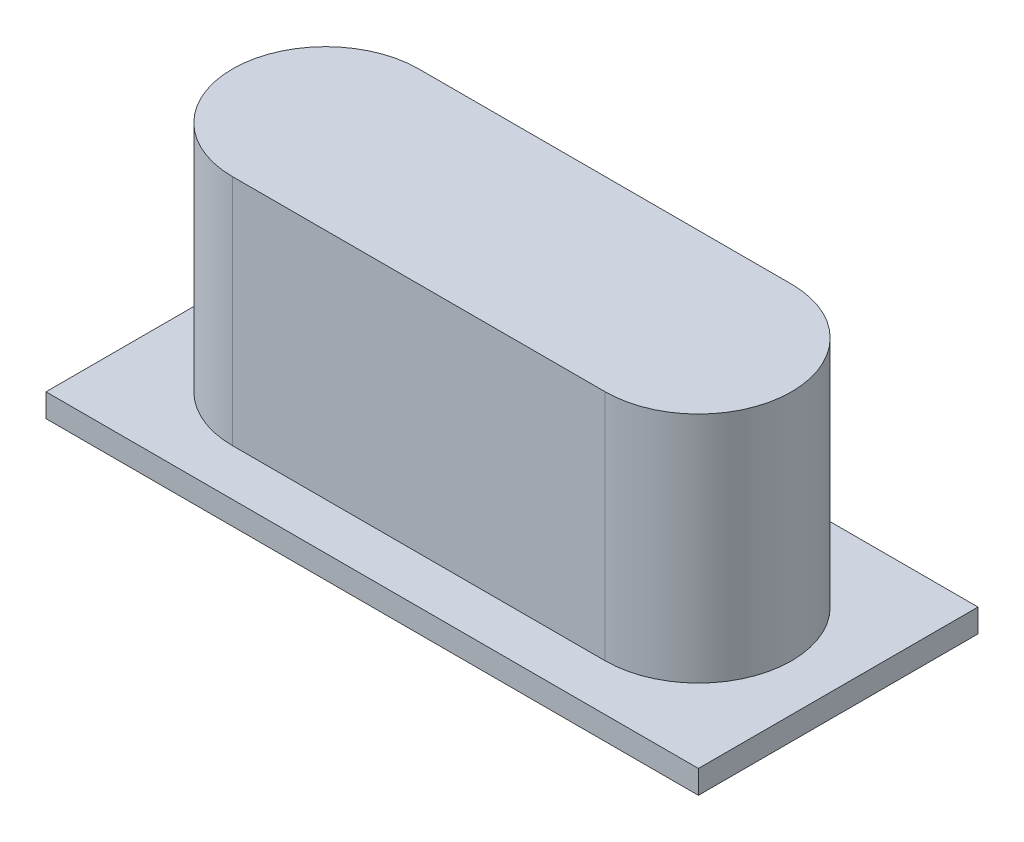
SolidWorks part; units mm, degrees
ref_plane "Front Plane" through (0, 0, 0) normal (0, 0, 1) x (1, 0, 0)
ref_plane "Top Plane" through (0, 0, 0) normal (0, 1, 0) x (1, 0, 0)
ref_plane "Right Plane" through (0, 0, 0) normal (1, 0, 0) x (0, 0, -1)
sketch "Sketch1" plane through (0, 0, 0) normal (0, 1, 0) x (1, 0, 0)
  line L1 (-3.5, -1.5) -> (3.5, -1.5)
  line L2 (-3.5, -1.5) -> (-3.5, 1.5)
  line L3 (-3.5, 1.5) -> (3.5, 1.5)
  line L4 (3.5, -1.5) -> (3.5, 1.5)
  line L5 (-3.5, -1.5) -> (3.5, 1.5) construction
  line L6 (-3.5, 1.5) -> (3.5, -1.5) construction
  point P0 (0, 0)
  dimension "D1" = 7
  dimension "D2" = 3
extrude "Boss-Extrude1" add sketch "Sketch1" along normal blind 0.25
sketch "Sketch2" plane through (0, 0.25, 0) normal (0, 1, 0) x (1, 0, 0)
  line L0 (0, 1.5) -> (0, -1.5) construction
  line L1 (3.5, 1.5) -> (-3.5, 1.5) construction
  line L2 (-3.5, -1.5) -> (3.5, -1.5) construction
  line L3 (-3.5, 0) -> (3.5, 0) construction
  line L4 (-3.5, 1.5) -> (-3.5, -1.5) construction
  line L5 (3.5, -1.5) -> (3.5, 1.5) construction
  line L6 (2, 0) -> (-2, 0) construction
  line L7 (2, -1) -> (-2, -1)
  line L8 (2, 1) -> (-2, 1)
  arc A0 (2, -1) -> (2, 1) centre (2, 0) ccw
  arc A1 (-2, 1) -> (-2, -1) centre (-2, 0) ccw
  point P14 (0, 0)
extrude "Boss-Extrude2" add sketch "Sketch2" along normal blind 2.5
